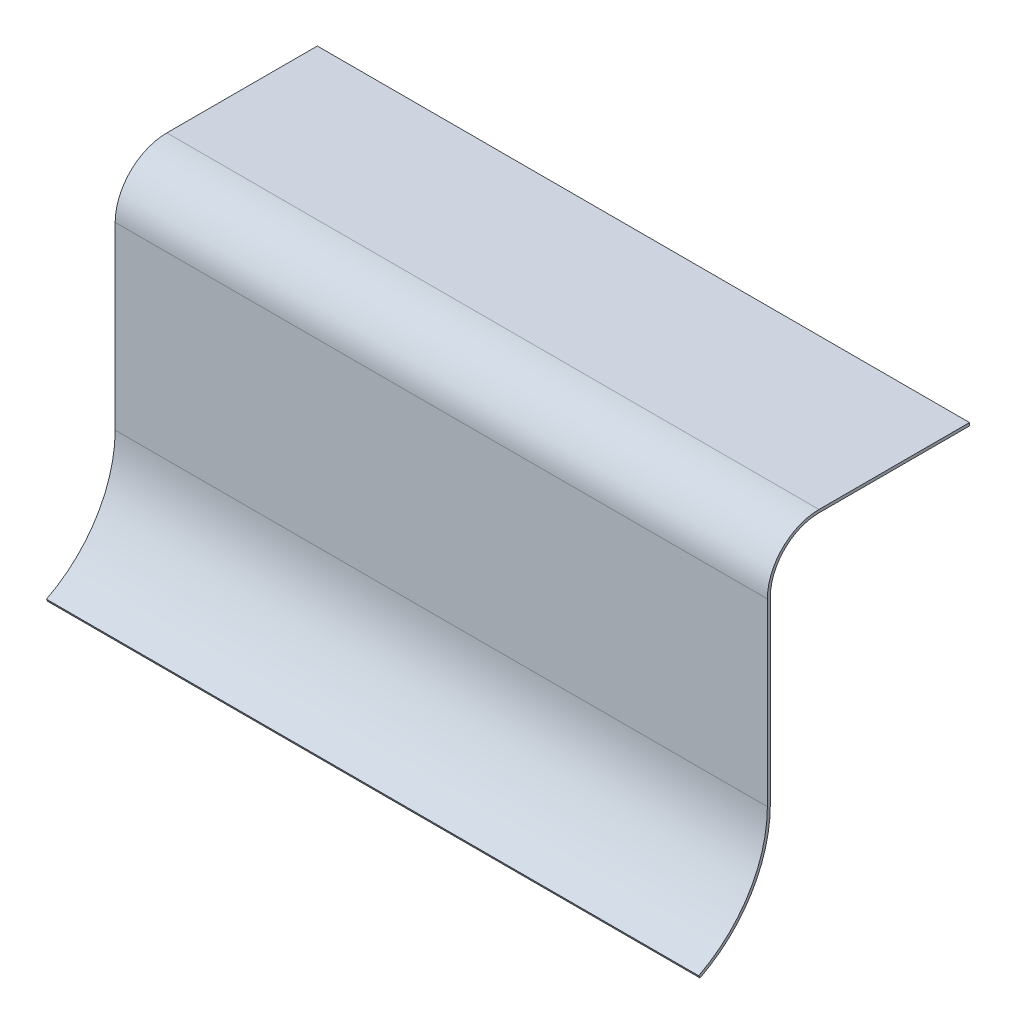
SolidWorks part; units mm, degrees
ref_plane "Front Plane" through (0, 0, 0) normal (0, 0, 1) x (1, 0, 0)
ref_plane "Top Plane" through (0, 0, 0) normal (0, 1, 0) x (1, 0, 0)
ref_plane "Right Plane" through (0, 0, 0) normal (1, 0, 0) x (0, 0, -1)
sketch "Sketch2" plane through (0, 0, 0) normal (1, 0, 0) x (0, 0, -1)
  line L0 (-25.4, -116.4948) -> (-25.4, -25.4) construction
  line L1 (-25.4, -116.4948) -> (-25.4, -25.4)
  line L2 (0, 0) -> (76.2, 0) construction
  line L3 (0, 0) -> (76.2, 0)
  arc A0 (-60.5807, -173.9) -> (-25.4, -116.4948) centre (-89.825, -116.4948) ccw construction
  arc A1 (-60.5807, -173.9) -> (-25.4, -116.4948) centre (-89.825, -116.4948) ccw
  arc A2 (0, 0) -> (-25.4, -25.4) centre (0, -25.4) ccw construction
  arc A3 (0, 0) -> (-25.4, -25.4) centre (0, -25.4) ccw
extrude "Extrude-Thin1" add sketch "Sketch2" along normal mid plane 330.2 thin thin type mid plane wall 1.5
